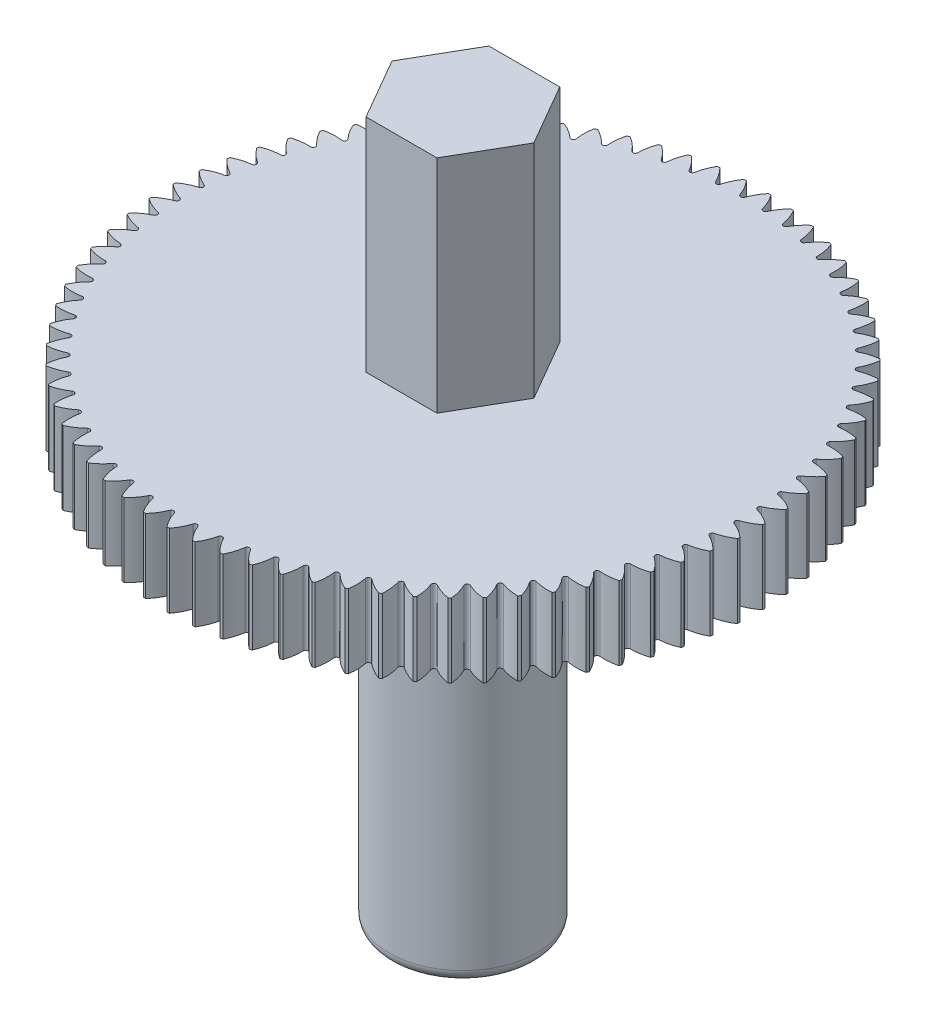
SolidWorks part; units mm, degrees
ref_plane "Front Plane" through (0, 0, 0) normal (0, 0, 1) x (1, 0, 0)
ref_plane "Top Plane" through (0, 0, 0) normal (0, 1, 0) x (1, 0, 0)
ref_plane "Right Plane" through (0, 0, 0) normal (1, 0, 0) x (0, 0, -1)
sketch "Sketch1" plane through (0, 0, 0) normal (0, 0, 1) x (1, 0, 0)
  line L0 (0, 0) -> (0, 29)
  line L1 (0, 0) -> (3, 0)
  line L2 (3, 0) -> (3, 17)
  line L3 (3, 17) -> (12, 17)
  line L4 (12, 17) -> (12, 20)
  line L5 (12, 20) -> (3, 20)
  line L6 (3, 20) -> (3, 29)
  line L7 (3, 29) -> (0, 29)
  dimension "D1" = 29
  dimension "D2" = 3
  dimension "D3" = 17
  dimension "D4" = 9
  dimension "D5" = 3
  dimension "D6" = 9
revolve "Revolve1" add sketch "Sketch1" angle 360 about L0
fillet "Fillet1" radius 0.5 1 edges at (0, 0, -3)
sketch "Sketch2" plane through (0, 29, 0) normal (0, 1, 0) x (1, 0, 0)
  line L1 (1.4434, -2.5) -> (2.8868, 0)
  line L2 (2.8868, 0) -> (1.4434, 2.5)
  line L3 (1.4434, 2.5) -> (-1.4434, 2.5)
  line L4 (-1.4434, 2.5) -> (-2.8868, 0)
  line L5 (-2.8868, 0) -> (-1.4434, -2.5)
  line L6 (-1.4434, -2.5) -> (1.4434, -2.5)
  circle A0 centre (0, 0) radius 3 construction
  circle A1 centre (0, 0) radius 3
  circle A2 centre (0, 0) radius 2.5 construction
  dimension "D1" = 5
extrude "Cut-Extrude1" cut sketch "Sketch2" against normal blind 9
sketch "Sketch3" plane through (0, 20, 0) normal (0, 1, 0) x (1, 0, 0)
  line L0 (0, 0) -> (0, 16.1739) construction
  circle A0 centre (0, 0) radius 12 construction
  arc A1 (0.45, 11.9916) -> (-0.45, 11.9916) centre (0, 0) ccw
  arc A2 (-0.45, 11.9916) -> (-0.0942, 11.3714) centre (-1.979, 10.7023) cw
  arc A3 (0.45, 11.9916) -> (0.0942, 11.3714) centre (1.979, 10.7023) ccw
  arc A4 (-0.0942, 11.3714) -> (0.0942, 11.3714) centre (0, 11.4049) ccw
  point P11 (0, 0)
  point P14 (0, 10.9916)
  dimension "D3" = 2
  dimension "D4" = 2
  dimension "D5" = 0.1
  dimension "D1" = 0.9
  dimension "D2" = 1
extrude "Cut-Extrude2" cut sketch "Sketch3" against normal blind 4
pattern_circular "CirPattern1" count 75 over 360 about axis through (0, 0, 0) along (0, 1, 0) of "Cut-Extrude2"
